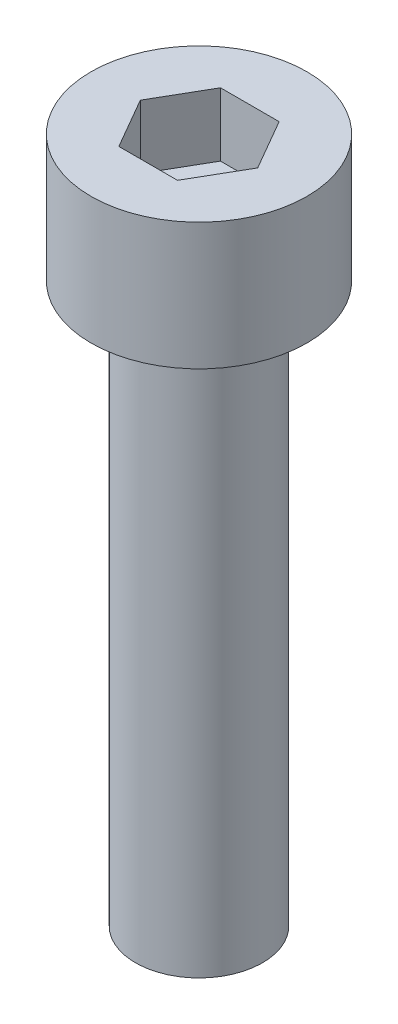
SolidWorks part; units mm, degrees
material "AISI 304"
ref_plane "前视基准面" through (0, 0, 0) normal (0, 0, 1) x (1, 0, 0)
ref_plane "上视基准面" through (0, 0, 0) normal (0, 1, 0) x (1, 0, 0)
ref_plane "右视基准面" through (0, 0, 0) normal (1, 0, 0) x (0, 0, -1)
sketch "草图1" plane through (0, 0, 0) normal (0, 1, 0) x (1, 0, 0)
  circle A0 centre (0, 0) radius 4.25
  dimension "D1" = 8.5
extrude "凸台-拉伸1" add sketch "草图1" along normal blind 5
sketch "草图2" plane through (0, 5, 0) normal (0, 1, 0) x (1, 0, 0)
  line L1 (2.3094, 0) -> (1.1547, 2)
  line L2 (1.1547, 2) -> (-1.1547, 2)
  line L3 (-1.1547, 2) -> (-2.3094, 0)
  line L4 (-2.3094, 0) -> (-1.1547, -2)
  line L5 (-1.1547, -2) -> (1.1547, -2)
  line L6 (1.1547, -2) -> (2.3094, 0)
  circle A0 centre (0, 0) radius 2 construction
  dimension "D1" = 4
extrude "切除-拉伸1" cut sketch "草图2" against normal blind 2.5
sketch "草图3" plane through (0, 0, 0) normal (0, -1, 0) x (1, 0, 0)
  circle A0 centre (0, 0) radius 2.5
  dimension "D1" = 5
extrude "凸台-拉伸2" add sketch "草图3" along normal blind 22
